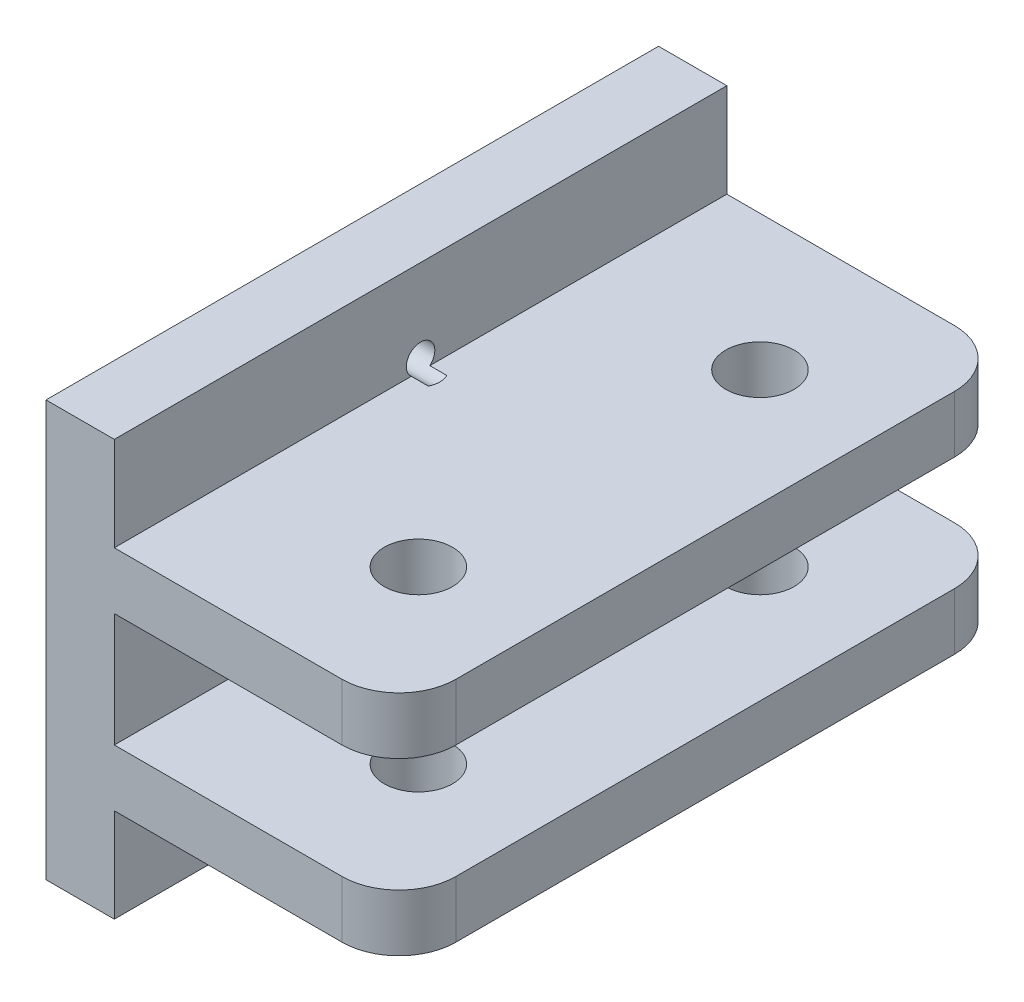
SolidWorks part; units mm, degrees
ref_plane "前视基准面" through (0, 0, 0) normal (0, 0, 1) x (1, 0, 0)
ref_plane "上视基准面" through (0, 0, 0) normal (0, 1, 0) x (1, 0, 0)
ref_plane "右视基准面" through (0, 0, 0) normal (1, 0, 0) x (0, 0, -1)
sketch "草图1" plane through (0, 0, 0) normal (1, 0, 0) x (0, 0, -1)
  line L1 (26.9, -18.25) -> (-26.9, -18.25)
  line L2 (26.9, -18.25) -> (26.9, 18.25)
  line L3 (26.9, 18.25) -> (-26.9, 18.25)
  line L4 (-26.9, -18.25) -> (-26.9, 18.25)
  line L5 (26.9, -18.25) -> (-26.9, 18.25) construction
  line L6 (26.9, 18.25) -> (-26.9, -18.25) construction
  point P0 (0, 0)
  dimension "D1" = 53.8
  dimension "D2" = 36.5
extrude "凸台-拉伸1" add sketch "草图1" along normal blind 6
sketch "草图2" plane through (6, 0, 0) normal (1, 0, 0) x (0, 0, -1)
  line L0 (26.9, -18.25) -> (26.9, 18.25) construction
  line L1 (-26.9, 10) -> (26.9, 10)
  line L2 (-26.9, 10) -> (-26.9, -10)
  line L3 (-26.9, -10) -> (26.9, -10)
  line L4 (26.9, 10) -> (26.9, -10)
  line L5 (-26.9, 10) -> (26.9, -10) construction
  line L6 (-26.9, -10) -> (26.9, 10) construction
  point P0 (0, 0)
  dimension "D1" = 20
extrude "凸台-拉伸2" add sketch "草图2" along normal blind 25
sketch "草图3" plane through (31, 0, 0) normal (1, 0, 0) x (0, 0, -1)
  line L0 (-26.9, 10) -> (-26.9, -10) construction
  line L1 (26.9, -5) -> (-26.9, -5)
  line L2 (26.9, -5) -> (26.9, 5)
  line L3 (26.9, 5) -> (-26.9, 5)
  line L4 (-26.9, -5) -> (-26.9, 5)
  line L5 (26.9, -5) -> (-26.9, 5) construction
  line L6 (26.9, 5) -> (-26.9, -5) construction
  point P0 (0, 0)
  dimension "D1" = 10
extrude "切除-拉伸1" cut sketch "草图3" against normal up to surface (25 mm away) up to face at (6, -14.125, 0)
hole_wizard "M3 螺纹孔1" positions "草图4" profile "草图5" tap size "M3" standard "ISO"
sketch "草图4" plane through (0, 0, 0) normal (-1, 0, 0) x (0, 0, 1)
  point P0 (-10.95, 0)
  point P3 (0, 10.95)
  point P6 (0, 0)
  point P9 (0, -10.95)
  point P12 (10.95, 0)
sketch "草图5" plane through (0, 0, -10.95) normal (0, 1, 0) x (0, 0, 1)
  line L0 (0, 0) -> (0, 8.2511)
  line L1 (0, 8.2511) -> (1.25, 7.5)
  line L2 (1.25, 7.5) -> (1.25, 0)
  line L5 (1.25, 0) -> (0, 0)
  line L10 (0, 8.2511) -> (-1.25, 7.5) construction
  line L11 (0, -6.35) -> (0, 107.95) construction
  dimension "螺纹孔钻头直径" = 2.5
  dimension "螺纹孔钻头深度" = 7.5
  dimension "导头角度" = 118
cosmetic thread "孔螺蚊线1" parameters "D1"=6, "D2"=3
cosmetic thread "孔螺蚊线2" parameters "D1"=6, "D2"=3
cosmetic thread "孔螺蚊线3" parameters "D1"=6, "D2"=3
cosmetic thread "孔螺蚊线4" parameters "D1"=6, "D2"=3
cosmetic thread "孔螺蚊线5" parameters "D1"=6, "D2"=3
sketch "草图6" plane through (0, -10, 0) normal (0, -1, 0) x (1, 0, 0)
  circle A0 centre (20.8061, 15) radius 3
  circle A1 centre (20.8061, -15) radius 3
  dimension "D1" = 6
extrude "切除-拉伸2" cut sketch "草图6" against normal through all
fillet "圆角1" radius 5 4 edges at (31, -7.5, -26.9) (31, -7.5, 26.9) (31, 7.5, 26.9) (31, 7.5, -26.9)
